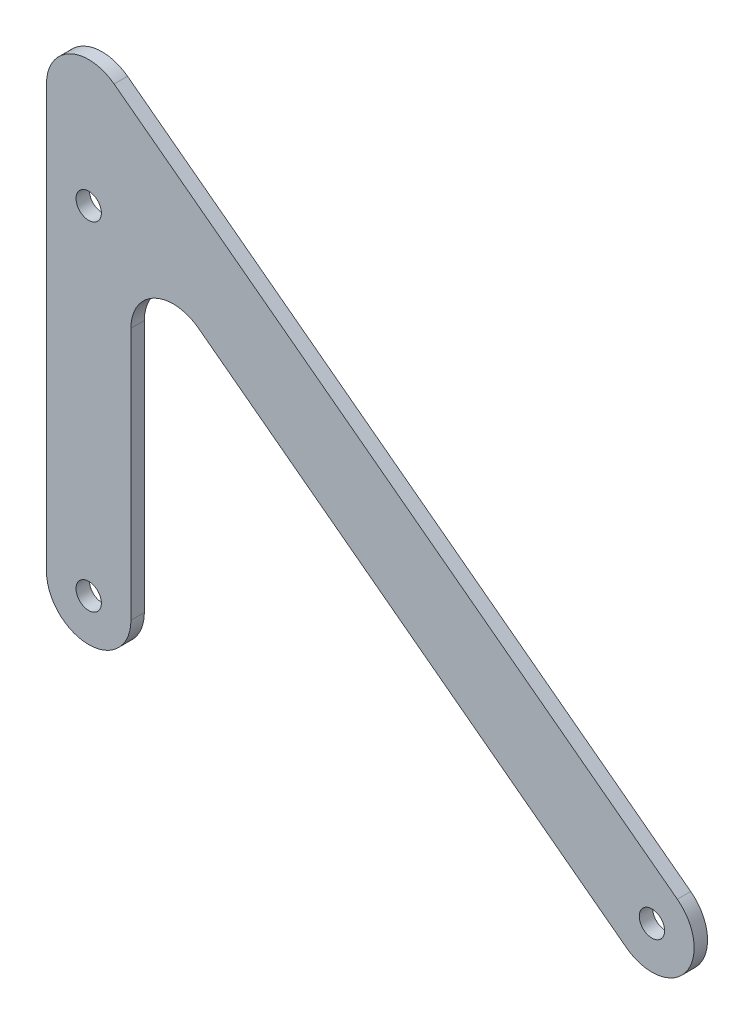
SolidWorks part; units mm, degrees
ref_plane "Front Plane" through (0, 0, 0) normal (0, 0, 1) x (1, 0, 0)
ref_plane "Top Plane" through (0, 0, 0) normal (0, 1, 0) x (1, 0, 0)
ref_plane "Right Plane" through (0, 0, 0) normal (1, 0, 0) x (0, 0, -1)
sketch "Sketch1" plane through (0, 0, 0) normal (0, 0, 1) x (1, 0, 0)
  line L0 (0, 0) -> (0, 100) construction
  line L1 (0, 100) -> (133.3721, -0.5031) construction
  line L2 (10, 0) -> (10, 79.9431)
  line L3 (10, 79.9431) -> (127.354, -8.4895)
  line L4 (-10, 0) -> (-10, 120.0569)
  line L5 (-10, 120.0569) -> (139.3903, 7.4832)
  arc A0 (10, 0) -> (-10, 0) centre (0, 0) cw
  arc A1 (139.3903, 7.4832) -> (127.354, -8.4895) centre (133.3721, -0.5031) cw
  circle A2 centre (0, 0) radius 3
  circle A3 centre (133.3721, -0.5031) radius 3
  dimension "D6" = 10
  dimension "D7" = 6
  dimension "D1" = 100
  dimension "D2" = 53
  dimension "D3" = 167
  dimension "D4" = 10
  dimension "D5" = 10
extrude "Boss-Extrude1" add sketch "Sketch1" along normal blind 3.175
fillet "Fillet1" radius 10 2 edges at (10, 79.9431, 1.5875) (-10, 120.0569, 1.5875)
sketch "Sketch2" plane through (0, 0, 3.175) normal (0, 0, 1) x (1, 0, 0)
  circle A0 centre (0, 80) radius 3
  dimension "D1" = 6
  dimension "D2" = 80
extrude "Cut-Extrude1" cut sketch "Sketch2" against normal through all
ref_point "Point1"
